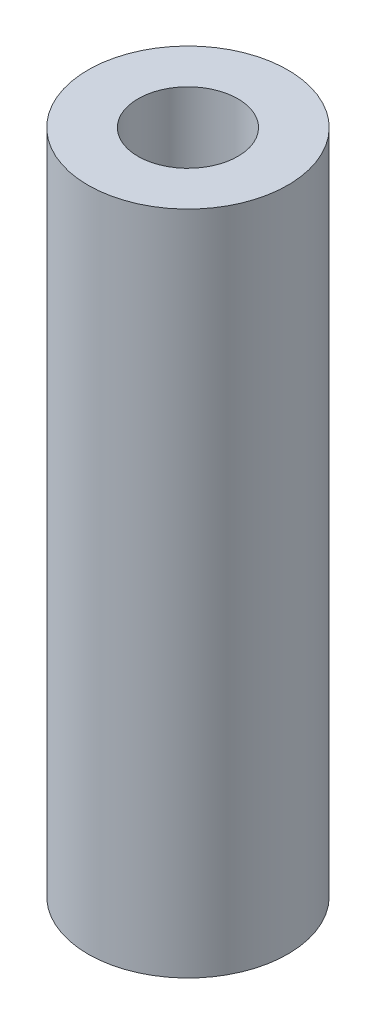
SolidWorks part; units mm, degrees
material "Delrin 2700 NC010, Low Viscosity Acetal Copolymer (SS)"
ref_plane "Front Plane" through (0, 0, 0) normal (0, 0, 1) x (1, 0, 0)
ref_plane "Top Plane" through (0, 0, 0) normal (0, 1, 0) x (1, 0, 0)
ref_plane "Right Plane" through (0, 0, 0) normal (1, 0, 0) x (0, 0, -1)
sketch "Sketch1" plane through (0, 0, 0) normal (0, 1, 0) x (1, 0, 0)
  circle A0 centre (0, 0) radius 3
  circle A1 centre (0, 0) radius 1.5
  dimension "D1" = 3
  dimension "D2" = 6
extrude "Boss-Extrude1" add sketch "Sketch1" along normal blind 20
